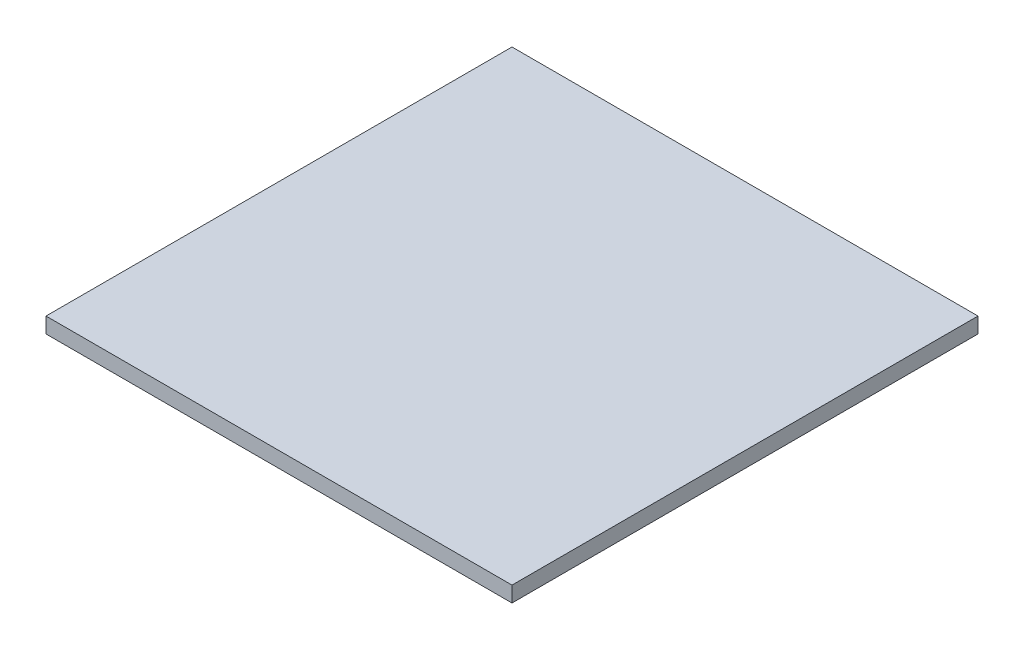
SolidWorks part; units mm, degrees
material "1060-H14"
ref_plane "Front Plane" through (0, 0, 0) normal (0, 0, 1) x (1, 0, 0)
ref_plane "Top Plane" through (0, 0, 0) normal (0, 1, 0) x (1, 0, 0)
ref_plane "Right Plane" through (0, 0, 0) normal (1, 0, 0) x (0, 0, -1)
sketch "Sketch1" plane through (0, 0, 0) normal (0, 1, 0) x (1, 0, 0)
  line L1 (-150, 150) -> (150, 150)
  line L2 (-150, 150) -> (-150, -150)
  line L3 (-150, -150) -> (150, -150)
  line L4 (150, 150) -> (150, -150)
  line L5 (-150, 150) -> (150, -150) construction
  line L6 (-150, -150) -> (150, 150) construction
  point P0 (0, 0)
  dimension "D1" = 300
extrude "Boss-Extrude1" add sketch "Sketch1" along normal blind 10
